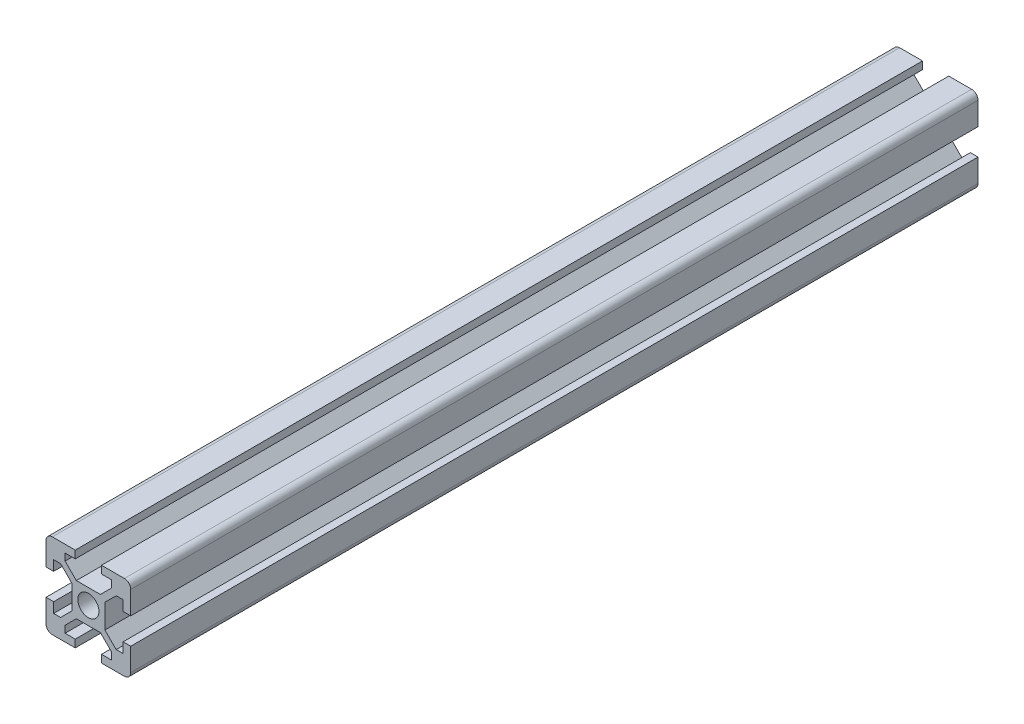
SolidWorks part; units mm, degrees
ref_plane "Front Plane" through (0, 0, 0) normal (0, 0, 1) x (1, 0, 0)
ref_plane "Top Plane" through (0, 0, 0) normal (0, 1, 0) x (1, 0, 0)
ref_plane "Right Plane" through (0, 0, 0) normal (1, 0, 0) x (0, 0, -1)
sketch "Sketch1" plane through (0, 0, 0) normal (0, 0, 1) x (1, 0, 0)
  line L0 (0, 13.3843) -> (0, -12.9126) construction
  line L1 (-14.4653, 0) -> (14.4653, 0) construction
  line L2 (2.8393, 3.9) -> (5.5, 6.5607)
  line L7 (-10, 10) -> (10, -10) construction
  line L8 (-10, -10) -> (10, 10) construction
  line L9 (-5.5, 8.2) -> (-3.1, 8.2)
  line L10 (-5.9626, 4.902) -> (-4.902, 5.9626) construction
  line L11 (-2.8393, 3.9) -> (-5.5, 6.5607)
  line L12 (-5.5, 8.2) -> (-5.5, 6.5607)
  line L13 (-2.8393, 3.9) -> (2.8393, 3.9)
  line L14 (5.5, 8.2) -> (5.5, 6.5607)
  line L17 (-3.1, 9.5) -> (3.1, 9.5) construction
  line L23 (3.1, 8.2) -> (5.5, 8.2)
  line L27 (-8.2, -3.1) -> (-8.2, -5.5)
  line L28 (-8.2, -5.5) -> (-6.5607, -5.5)
  line L29 (-3.9, -2.8393) -> (-6.5607, -5.5)
  line L30 (-3.9, 2.8393) -> (-3.9, -2.8393)
  line L31 (-3.9, 2.8393) -> (-6.5607, 5.5)
  line L32 (-8.2, 5.5) -> (-6.5607, 5.5)
  line L33 (-8.2, 5.5) -> (-8.2, 3.1)
  line L40 (-3.1, -8.2) -> (-5.5, -8.2)
  line L41 (-5.5, -8.2) -> (-5.5, -6.5607)
  line L42 (-2.8393, -3.9) -> (-5.5, -6.5607)
  line L43 (2.8393, -3.9) -> (-2.8393, -3.9)
  line L44 (2.8393, -3.9) -> (5.5, -6.5607)
  line L45 (5.5, -8.2) -> (5.5, -6.5607)
  line L46 (5.5, -8.2) -> (3.1, -8.2)
  line L53 (8.2, -5.5) -> (8.2, -3.1)
  line L54 (8.2, -5.5) -> (6.5607, -5.5)
  line L55 (3.9, -2.8393) -> (6.5607, -5.5)
  line L56 (3.9, -2.8393) -> (3.9, 2.8393)
  line L57 (3.9, 2.8393) -> (6.5607, 5.5)
  line L58 (8.2, 5.5) -> (6.5607, 5.5)
  line L59 (8.2, 3.1) -> (8.2, 5.5)
  line L68 (-3.1, -8.2) -> (-3.1, -10)
  line L69 (-3.1, -10) -> (-8.5, -10)
  line L70 (-8.2, -3.1) -> (-10, -3.1)
  line L71 (-10, -3.1) -> (-10, -8.5)
  line L72 (-8.2, 3.1) -> (-10, 3.1)
  line L73 (-10, 3.1) -> (-10, 8.5)
  line L74 (-3.1, 8.2) -> (-3.1, 10)
  line L75 (-3.1, 10) -> (-8.5, 10)
  line L76 (3.1, 8.2) -> (3.1, 10)
  line L77 (3.1, 10) -> (8.5, 10)
  line L78 (8.2, 3.1) -> (10, 3.1)
  line L79 (10, 3.1) -> (10, 8.5)
  line L80 (8.2, -3.1) -> (10, -3.1)
  line L81 (10, -3.1) -> (10, -8.5)
  line L82 (3.1, -8.2) -> (3.1, -10)
  line L83 (3.1, -10) -> (8.5, -10)
  arc A0 (8.5, 10) -> (10, 8.5) centre (8.5, 8.5) cw
  arc A1 (8.5, -10) -> (10, -8.5) centre (8.5, -8.5) ccw
  arc A2 (-10, -8.5) -> (-8.5, -10) centre (-8.5, -8.5) ccw
  arc A3 (-8.5, 10) -> (-10, 8.5) centre (-8.5, 8.5) ccw
  circle A4 centre (0, 0.2358) radius 2.5
  point P5 (0, 0)
  point P30 (-5.4323, 5.4323)
  point P38 (0, 9.5)
  dimension "D3" = 1.5
  dimension "D15" = 5
  dimension "D1" = 20
  dimension "D2" = 20
  dimension "D5" = 11
  dimension "D7" = 1.5
  dimension "D8" = 90
  dimension "D14" = 45
extrude "Boss-Extrude1" add sketch "Sketch1" along normal blind 200
